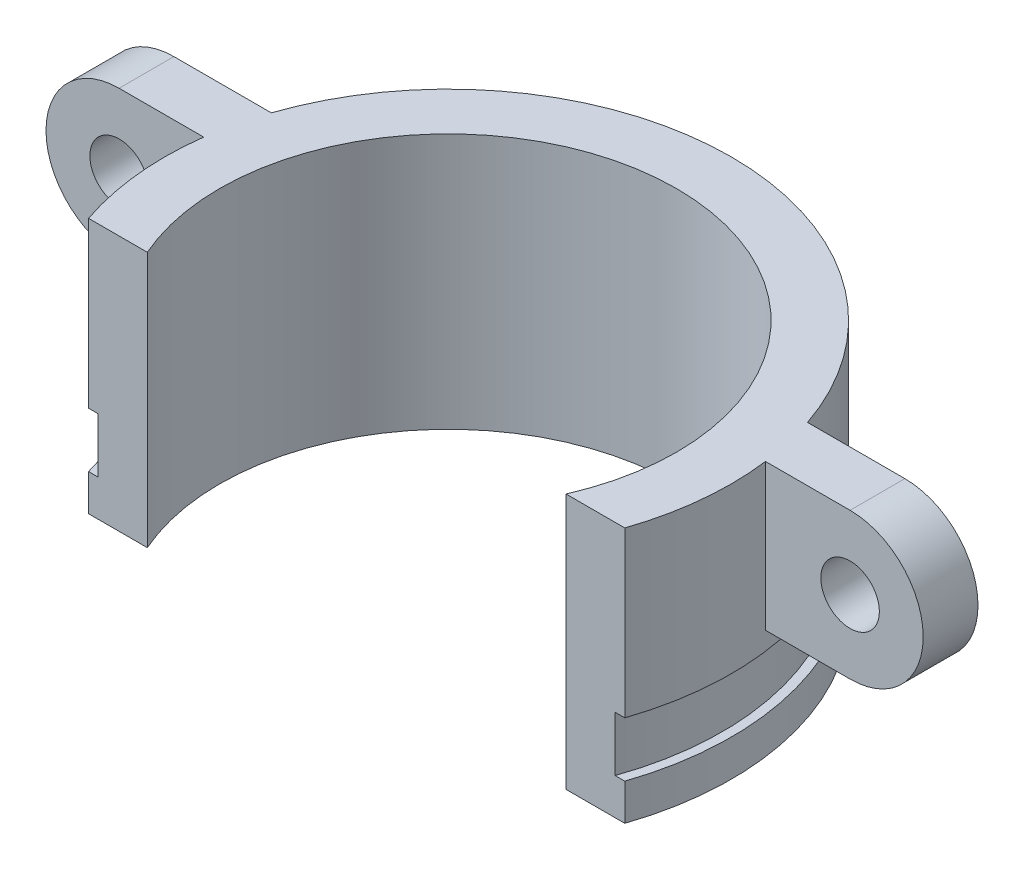
SolidWorks part; units mm, degrees
ref_plane "Plano frontal" through (0, 0, 0) normal (0, 0, 1) x (1, 0, 0)
ref_plane "Plano superior" through (0, 0, 0) normal (0, 1, 0) x (1, 0, 0)
ref_plane "Plano direito" through (0, 0, 0) normal (1, 0, 0) x (0, 0, -1)
sketch "Esboço1" plane through (0, 0, 0) normal (0, 0, 1) x (1, 0, 0)
  line L0 (0, 0) -> (0, 33.0251) construction
  line L1 (15, 37) -> (15.5, 37)
  line L2 (12.5, 50) -> (12.5, 0)
  line L3 (12.5, 0) -> (15.5, 0)
  line L4 (15.5, 0) -> (15.5, 10)
  line L5 (15.5, 10) -> (15, 10)
  line L6 (15, 10) -> (15, 13)
  line L7 (15, 13) -> (15.5, 13)
  line L8 (15.5, 13) -> (15.5, 37)
  line L9 (12.5, 25) -> (30.7372, 25) construction
  line L10 (15, 40) -> (15, 37)
  line L11 (15.5, 40) -> (15, 40)
  line L12 (15.5, 50) -> (15.5, 40)
  line L13 (12.5, 50) -> (15.5, 50)
  point P4 (15.5, 25)
  dimension "D1" = 50
  dimension "D2" = 3
  dimension "D3" = 12
  dimension "D4" = 3
  dimension "D5" = 0.5
  dimension "D6" = 25
revolve "Revolução1" add sketch "Esboço1" angle 360 about L0
sketch "Esboço2" plane through (0, 50, 0) normal (0, 1, 0) x (1, 0, 0)
  line L0 (-14.6714, -5) -> (-11.4564, -5)
  line L1 (0, 0) -> (0, -19.0451) construction
  line L2 (14.6714, -5) -> (11.4564, -5)
  circle A0 centre (0, 0) radius 15.5 construction
  circle A1 centre (0, 0) radius 12.5 construction
  circle M1 centre (0, 0) radius 12.5
  circle M2 centre (0, 0) radius 15.5
  dimension "D1" = 5
extrude "Corte-extrusão1" cut sketch "Esboço2" against normal through all both and the other way through all contours L1 L2 M1 M2 | L1 L0 M1 M2
sketch "Esboço3" plane through (0, 0, 0) normal (0, 0, 1) x (1, 0, 0)
  line L0 (-13.5, 49) -> (-20, 49)
  line L2 (-20, 41) -> (-13.5, 41)
  line L3 (-13.5, 41) -> (-13.5, 49)
  line L4 (0, 0) -> (0, 50) construction
  line L5 (12.5, 50) -> (-12.5, 50) construction
  line L6 (13.5, 41) -> (13.5, 49)
  line L7 (-30.0287, 25) -> (0, 25) construction
  line L8 (20, 41) -> (13.5, 41)
  line L9 (13.5, 49) -> (20, 49)
  line L10 (13.5, 1) -> (20, 1)
  line L11 (20, 9) -> (13.5, 9)
  line L12 (13.5, 9) -> (13.5, 1)
  line L13 (-13.5, 9) -> (-13.5, 1)
  line L14 (-20, 9) -> (-13.5, 9)
  line L15 (-13.5, 1) -> (-20, 1)
  line L16 (-15.5, 50) -> (-15.5, 40) construction
  arc A0 (-20, 49) -> (-20, 41) centre (-20, 45) ccw
  circle A1 centre (-20, 45) radius 1.6
  circle A2 centre (20, 45) radius 1.6
  arc A3 (20, 49) -> (20, 41) centre (20, 45) cw
  arc A4 (20, 1) -> (20, 9) centre (20, 5) ccw
  circle A5 centre (20, 5) radius 1.6
  circle A6 centre (-20, 5) radius 1.6
  arc A7 (-20, 1) -> (-20, 9) centre (-20, 5) cw
  dimension "D1" = 3.2
  dimension "D2" = 4
  dimension "D3" = 40
  dimension "D4" = 40
  dimension "D5" = 2
extrude "Ressalto-extrusão1" add sketch "Esboço3" against normal blind 3 from offset 2 offset against normal yes
sketch "Esboço4" plane through (0, 0, 0) normal (0, 0, 1) x (1, 0, 0)
  line L0 (-15.3704, 49) -> (-20, 49) construction
  line L1 (25.7993, 49) -> (-25.7993, 49)
  line L2 (25.7993, 49) -> (25.7993, 35)
  line L3 (25.7993, 35) -> (-25.7993, 35)
  line L4 (-25.7993, 49) -> (-25.7993, 35)
  line L6 (33.7529, 52.3365) -> (-33.6192, 52.3365)
  line L7 (33.7529, 52.3365) -> (33.7529, -2.7375)
  line L8 (33.7529, -2.7375) -> (-33.6192, -2.7375)
  line L9 (-33.6192, 52.3365) -> (-33.6192, -2.7375)
  dimension "D1" = 14
extrude "Corte-extrusão2" cut sketch "Esboço4" against normal through all both and the other way through all
